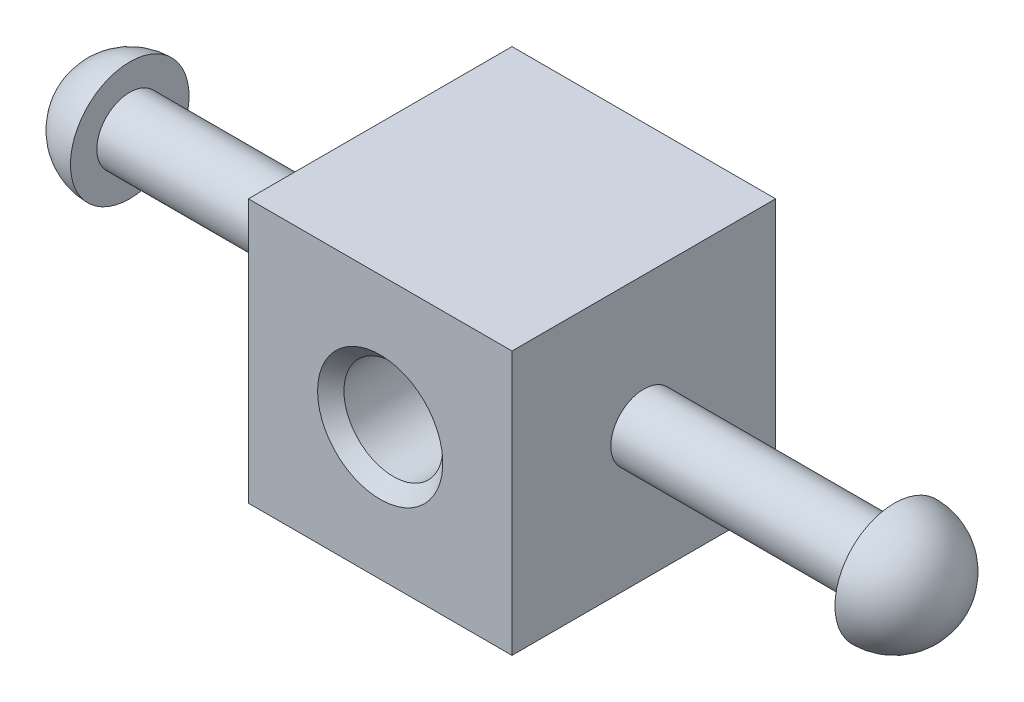
SolidWorks part; units mm, degrees
material "AISI 1020"
ref_plane "Front Plane" through (0, 0, 0) normal (0, 0, 1) x (1, 0, 0)
ref_plane "Top Plane" through (0, 0, 0) normal (0, 1, 0) x (1, 0, 0)
ref_plane "Right Plane" through (0, 0, 0) normal (1, 0, 0) x (0, 0, -1)
sketch "Sketch1" plane through (0, 0, 0) normal (0, 0, 1) x (1, 0, 0)
  line L0 (0, 0) -> (63.2872, 0) construction
  line L1 (5.715, 5.715) -> (5.715, 3.175)
  line L2 (5.715, 3.175) -> (79.375, 3.175)
  line L3 (0, 0) -> (0, 12.1658) construction
  line L4 (42.545, 3.175) -> (42.545, 0) construction
  line L5 (79.375, 5.715) -> (79.375, 3.175)
  line L6 (0, 0) -> (85.09, 0)
  arc A0 (0, 0) -> (5.715, 5.715) centre (5.715, 0) cw
  arc A1 (85.09, 0) -> (79.375, 5.715) centre (79.375, 0) ccw
  dimension "D2" = 5.715
  dimension "D1" = 36.83
  dimension "D3" = 6.35
  dimension "D4" = 11.43
revolve "Revolve1" add sketch "Sketch1" angle 360 about L6
sketch "Sketch2" plane through (0, 0, 0) normal (0, 0, 1) x (1, 0, 0)
  line L0 (5.715, -5.715) -> (5.715, 5.715) construction
  line L1 (29.845, -12.7) -> (55.245, -12.7)
  line L2 (29.845, -12.7) -> (29.845, 12.7)
  line L3 (29.845, 12.7) -> (55.245, 12.7)
  line L4 (55.245, -12.7) -> (55.245, 12.7)
  line L5 (29.845, -12.7) -> (55.245, 12.7) construction
  line L6 (29.845, 12.7) -> (55.245, -12.7) construction
  point P0 (42.545, 0)
  dimension "D1" = 36.83
  dimension "D2" = 25.4
  dimension "D3" = 25.4
extrude "Boss-Extrude1" add sketch "Sketch2" along normal mid plane 25.4
sketch "Sketch3" plane through (0, 0, 12.7) normal (0, 0, 1) x (1, 0, 0)
  line L0 (55.245, 12.7) -> (29.845, 12.7) construction
  circle A0 centre (42.545, 0) radius 4.7625
  point P4 (42.545, 12.7)
  dimension "D1" = 9.525
extrude "Cut-Extrude1" cut sketch "Sketch3" against normal through all
chamfer "Chamfer1" distance 1.27 angle 45 2 edges at (47.3075, 0, -12.7) (47.3075, 0, 12.7)
